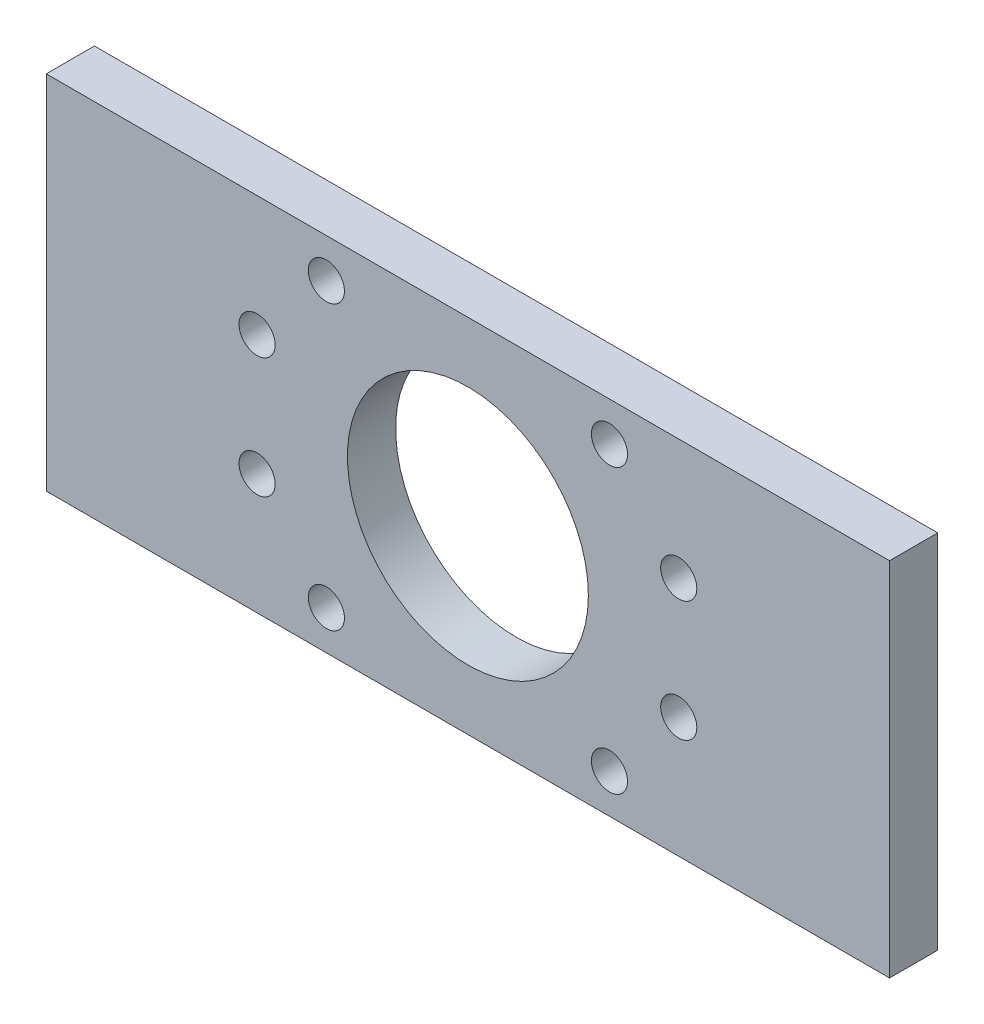
SolidWorks part; units mm, degrees
ref_plane "Plan de face" through (0, 0, 0) normal (0, 0, 1) x (1, 0, 0)
ref_plane "Plan de dessus" through (0, 0, 0) normal (0, 1, 0) x (1, 0, 0)
ref_plane "Plan de droite" through (0, 0, 0) normal (1, 0, 0) x (0, 0, -1)
sketch "Esquisse1" plane through (0, 0, 0) normal (0, 0, 1) x (1, 0, 0)
  line L1 (-87.5206, 42.1123) -> (52.4794, 42.1123)
  line L2 (-87.5206, 42.1123) -> (-87.5206, -17.8877)
  line L3 (-87.5206, -17.8877) -> (52.4794, -17.8877)
  line L4 (52.4794, 42.1123) -> (52.4794, -17.8877)
  line L5 (-17.5206, -17.8877) -> (-16.7719, -18.1551) construction
  dimension "D1" = 140
  dimension "D2" = 60
extrude "Boss.-Extru.1" add sketch "Esquisse1" along normal blind 8
sketch "Esquisse2" plane through (0, 0, 8) normal (0, 0, 1) x (1, 0, 0)
  line L0 (-17.5206, 42.1123) -> (-17.5206, -17.8877) construction
  line L1 (52.4794, 42.1123) -> (-87.5206, 42.1123) construction
  line L2 (-87.5206, -17.8877) -> (52.4794, -17.8877) construction
  line L3 (52.4794, 12.1123) -> (-87.5206, 12.1123) construction
  line L4 (-87.5206, 42.1123) -> (-87.5206, -17.8877) construction
  line L5 (52.4794, -17.8877) -> (52.4794, 42.1123) construction
  line L6 (5.9794, 42.1123) -> (5.9794, -17.8877) construction
  line L7 (-41.0206, 42.1123) -> (-41.0206, -17.8877) construction
  line L8 (-87.5206, 35.6123) -> (52.4794, 35.6123) construction
  line L9 (-87.5206, -11.3877) -> (52.4794, -11.3877) construction
  line L10 (-52.5206, 42.1123) -> (-52.5206, -17.8877) construction
  line L11 (17.4794, 42.1123) -> (17.4794, -17.8877) construction
  line L12 (-87.5206, 22.1123) -> (52.4794, 22.1123) construction
  line L13 (-87.5206, 2.1123) -> (52.4794, 2.1123) construction
  circle A0 centre (-17.5206, 12.1123) radius 20
  circle A1 centre (-41.0206, 35.6123) radius 3
  circle A2 centre (-41.0206, -11.3877) radius 3
  circle A3 centre (5.9794, 35.6123) radius 3
  circle A4 centre (5.9794, -11.3877) radius 3
  circle A5 centre (-52.5206, 22.1123) radius 3
  circle A6 centre (-52.5206, 2.1123) radius 3
  circle A7 centre (17.4794, 22.1123) radius 3
  circle A8 centre (17.4794, 2.1123) radius 3
  dimension "D1" = 40
  dimension "D6" = 6
  dimension "D7" = 6
  dimension "D8" = 6
  dimension "D9" = 6
  dimension "D14" = 6
  dimension "D15" = 6
  dimension "D16" = 6
  dimension "D17" = 6
  dimension "D2" = 23.5
  dimension "D3" = 23.5
  dimension "D4" = 23.5
  dimension "D5" = 23.5
  dimension "D10" = 20
  dimension "D11" = 20
  dimension "D12" = 35
  dimension "D13" = 35
extrude "Enlèv. mat.-Extru.1" cut sketch "Esquisse2" against normal through all
